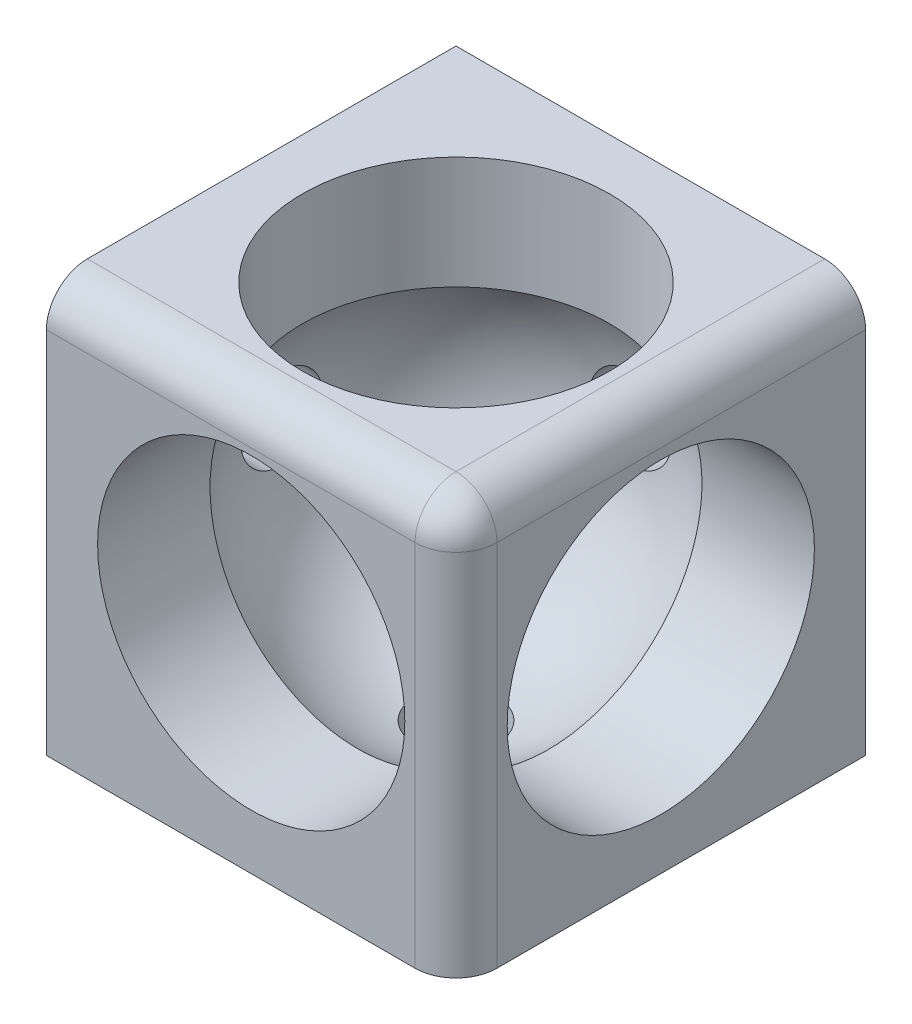
SolidWorks part; units mm, degrees
ref_plane "Ebene vorne" through (0, 0, 0) normal (0, 0, 1) x (1, 0, 0)
ref_plane "Ebene oben" through (0, 0, 0) normal (0, 1, 0) x (1, 0, 0)
ref_plane "Ebene rechts" through (0, 0, 0) normal (1, 0, 0) x (0, 0, -1)
sketch "Sketch1" plane through (0, 0, 0) normal (0, 1, 0) x (1, 0, 0)
  line L1 (20, -20) -> (-20, -20)
  line L2 (20, -20) -> (20, 20)
  line L3 (20, 20) -> (-20, 20)
  line L4 (-20, -20) -> (-20, 20)
  line L5 (20, -20) -> (-20, 20) construction
  line L6 (20, 20) -> (-20, -20) construction
  point P0 (0, 0)
  dimension "D1" = 40
  dimension "D2" = 40
extrude "Boss-Extrude1" add sketch "Sketch1" along normal mid plane 40
fillet "Fillet1" radius 4 3 edges at (0, 20, 20) (20, 0, 20) (20, 20, 0)
sketch "Sketch2" plane through (0, 0, 0) normal (0, 1, 0) x (1, 0, 0)
  line L0 (0, 20.9894) -> (0, -21.3876) construction
  line L1 (0, 17.5) -> (0, -17.5)
  arc A1 (0, 17.5) -> (0, -17.5) centre (0, 0) ccw
  dimension "D1" = 17.5
revolve "Cut-Revolve1" cut sketch "Sketch2" angle 360 about L0
sketch "Sketch12" plane through (0, 20, 0) normal (0, 1, 0) x (1, 0, 0)
  circle A0 centre (0, 0) radius 15
  dimension "D1" = 30
extrude "Cut-Extrude2" cut sketch "Sketch12" against normal blind 20
sketch "Sketch13" plane through (20, 0, 0) normal (1, 0, 0) x (0, 0, -1)
  circle A0 centre (0, 0) radius 15
  dimension "D1" = 30
extrude "Cut-Extrude3" cut sketch "Sketch13" against normal blind 20
sketch "Sketch14" plane through (0, 0, 20) normal (0, 0, 1) x (1, 0, 0)
  circle A0 centre (0, 0.3676) radius 15
  dimension "D1" = 30
extrude "Cut-Extrude4" cut sketch "Sketch14" against normal blind 20
sketch "Sketch15" plane through (0, 0, -20) normal (0, 0, -1) x (-1, 0, 0)
  circle A0 centre (0, 0) radius 4
  dimension "D1" = 8
extrude "Cut-Extrude5" cut sketch "Sketch15" against normal blind 20
sketch "Sketch16" plane through (0, -20, 0) normal (0, -1, 0) x (1, 0, 0)
  circle A0 centre (0, 0) radius 4
  dimension "D1" = 8
extrude "Cut-Extrude6" cut sketch "Sketch16" against normal blind 20
sketch "Sketch17" plane through (-20, 0, 0) normal (-1, 0, 0) x (0, 0, 1)
  circle A0 centre (0, 0) radius 4
  dimension "D1" = 8
extrude "Cut-Extrude7" cut sketch "Sketch17" against normal blind 20
